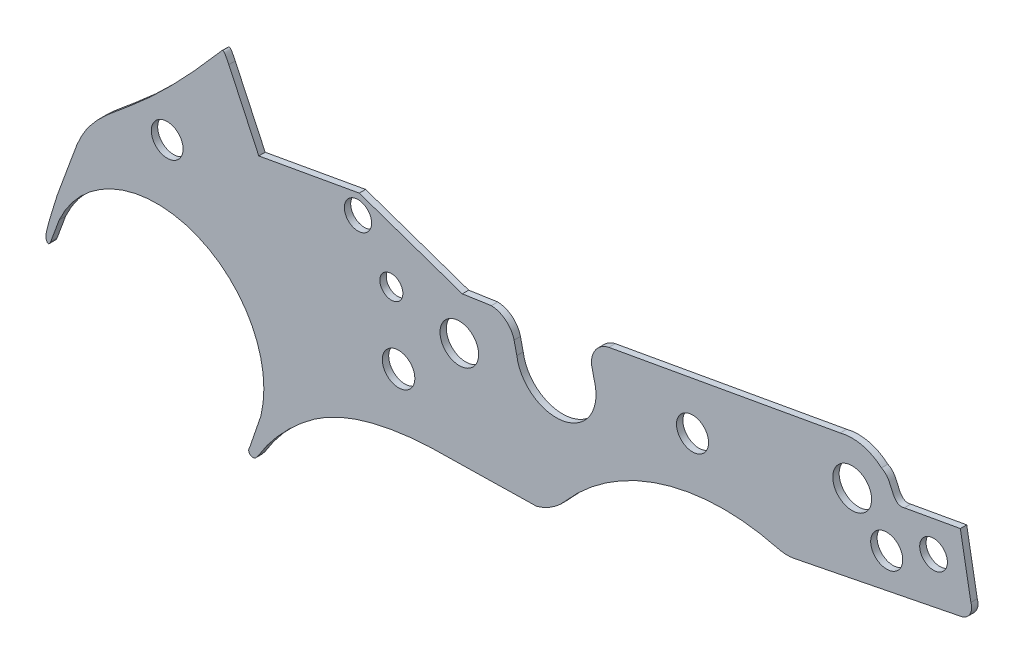
SolidWorks part; units mm, degrees
ref_plane "Plano frontal" through (0, 0, 0) normal (0, 0, 1) x (1, 0, 0)
ref_plane "Plano superior" through (0, 0, 0) normal (0, 1, 0) x (1, 0, 0)
ref_plane "Plano direito" through (0, 0, 0) normal (1, 0, 0) x (0, 0, -1)
sketch "Esboço1" plane through (0, 0, 0) normal (0, 0, 1) x (1, 0, 0)
  line L0 (244.5, 274) -> (1222.5, 274) construction
  line L3 (493.8163, 444.3581) -> (336.8371, 416.1756)
  line L4 (336.8371, 416.1756) -> (290.0355, 516.3686)
  line L7 (735.7897, 366.3785) -> (740.0612, 347.6021)
  line L10 (856.8027, 393.9078) -> (861.0162, 375.1183)
  line L11 (883.9506, 430.6875) -> (1245.3387, 495.5675)
  line L12 (1345.7117, 444.3581) -> (1433.211, 460.0669)
  line L13 (1449.6859, 368.3004) -> (1433.211, 460.0669)
  line L14 (1432.0519, 341.1705) -> (1178.4458, 290.6985)
  line L15 (602.8578, 155.751) -> (771.4681, 159.0464)
  line L16 (332.5591, 5.7781) -> (336.6858, 10.9907)
  line L17 (322.3689, 13.8453) -> (340.2002, 66.1093)
  line L18 (11.6682, 137.566) -> (24.9746, 173.6571)
  line L19 (493.8163, 444.3581) -> (654.9354, 388.555)
  line L20 (654.9354, 388.555) -> (700.294, 395.2703)
  arc A0 (700.294, 395.2703) -> (735.7897, 366.3785) centre (698.7484, 357.121) cw
  arc A1 (740.0612, 347.6021) -> (861.0162, 375.1183) centre (801.6376, 356.5293) ccw
  arc A2 (856.8027, 393.9078) -> (883.9506, 430.6875) centre (891.5191, 396.6919) cw
  arc A3 (1245.3387, 495.5675) -> (1310.0024, 480.4513) centre (1263.5567, 427.6334) cw
  arc A4 (1449.6859, 368.3004) -> (1432.0519, 341.1705) centre (1430.2194, 361.6574) cw
  arc A5 (1178.4458, 290.6985) -> (1147.056, 290.7924) centre (1162.9318, 351.1969) cw
  arc A6 (1147.056, 290.7924) -> (816.1447, 188.8838) centre (1063.645, -26.5724) ccw
  arc A7 (771.4681, 159.0464) -> (816.1447, 188.8838) centre (743.4327, 249.3912) ccw
  arc A8 (332.5591, 5.7781) -> (322.3689, 13.8453) centre (327.564, 9.938) cw
  arc A9 (340.2002, 66.1093) -> (24.9746, 173.6571) centre (177.4906, 104.9444) ccw
  circle A10 centre (193.6983, 366.3142) radius 24.8561
  circle A12 centre (555.2804, 237.0173) radius 25.4063
  circle A13 centre (650.2137, 319.2174) radius 30.1849
  circle A14 centre (491.8424, 413.2998) radius 21.3388
  circle A15 centre (543.9934, 342.5647) radius 17.9848
  circle A16 centre (1014.65, 379.4996) radius 25.0237
  circle A17 centre (1264.1481, 430.1293) radius 30.3488
  circle A18 centre (1318.1261, 372.5792) radius 25.0554
  circle A19 centre (1391.3097, 404.334) radius 21.6453
  spline S0 degree 3 poles (1310.0024, 480.4513) (1321.2, 475.0174) (1324.5591, 457.2304) (1335.7706, 441.5942) (1345.7117, 444.3581) knots 0 0 0 0 0.588753 1 1 1 1
  spline S1 degree 3 poles (602.8578, 155.751) (546.5859, 152.9347) (464.371, 137.6716) (381.4975, 70.8269) (350.3878, 34.1138) (336.6858, 10.9907) knots 0 0 0 0 0.545434 0.746227 1 1 1 1
  spline S2 degree 2 poles (11.6682, 137.566) (7.6746, 128.3439) (4.4427, 137.566) knots 0 0 0 1 1 1
  spline S3 degree 3 poles (4.4427, 137.566) (3.7572, 144.9101) (9.589, 165.5741) (18.5973, 197.4093) (31.6678, 232.5605) (42.7501, 261.9216) (50.9603, 286.1758) (59.8452, 305.1604) (71.5242, 324.3682) (97.3083, 353.0352) (175.534, 412.9129) (235.5999, 479.1806) (279.053, 529.6908) knots 0 0 0 0 0.044406 0.129466 0.202698 0.272841 0.321072 0.358779 0.400527 0.45776 0.592733 1 1 1 1
  spline S4 degree 3 poles (290.0355, 516.3686) (287.7123, 520.6446) (285.7094, 525.7108) (281.266, 531.6596) (279.053, 529.6908) knots 0 0 0 0 0.704309 1 1 1 1
  point P4 (654.9354, 384.9516)
  point P5 (700.294, 395.2703)
  point P6 (723.1323, 386.4652)
  point P7 (735.7897, 366.3785)
  point P8 (740.0612, 347.6021)
  point P9 (883.9506, 430.6875)
  point P10 (862.5528, 355.6607)
  point P14 (1245.3387, 495.5675)
  point P16 (1310.0024, 480.4513)
  point P18 (1327.8773, 454.8186)
  point P19 (1332.5073, 447.6163)
  point P20 (1345.7117, 444.3581)
  point P21 (1391.7824, 452.9217)
  point P22 (1427.4966, 459.1996)
  point P25 (1449.6859, 368.3004)
  point P26 (1446.7507, 349.5336)
  point P27 (1432.0519, 341.1705)
  point P28 (1178.4458, 290.6985)
  point P30 (1147.056, 290.7924)
  point P31 (771.4681, 159.0464)
  point P37 (816.1447, 188.8838)
  point P39 (602.8578, 155.751)
  point P40 (516.2613, 143.7184)
  point P41 (437.2844, 112.1277)
  point P42 (387.1685, 73.1336)
  point P43 (357.4722, 40.9327)
  point P44 (336.6858, 10.9907)
  point P45 (332.5591, 5.7781)
  point P48 (323.2198, 16.4206)
  point P49 (326.4777, 435.9702)
  point P52 (179.2117, 422.3133)
  point P53 (139.3397, 386.4652)
  point P54 (110.8745, 362.3485)
  point P55 (89.0863, 343.1236)
  point P56 (70.6374, 321.8755)
  point P57 (59.8478, 304.4134)
  point P58 (51.9735, 287.6293)
  point P59 (43.7999, 265.3692)
  point P60 (31.8678, 233.0118)
  point P61 (19.7069, 199.1217)
  point P62 (7.7485, 159.0464)
  point P63 (4.4427, 143.7184)
  point P64 (4.4427, 137.566)
  point P65 (7.7485, 132.9597)
  point P66 (11.6682, 137.566)
extrude "Ressalto-extrusão1" add sketch "Esboço1" along normal blind 10
